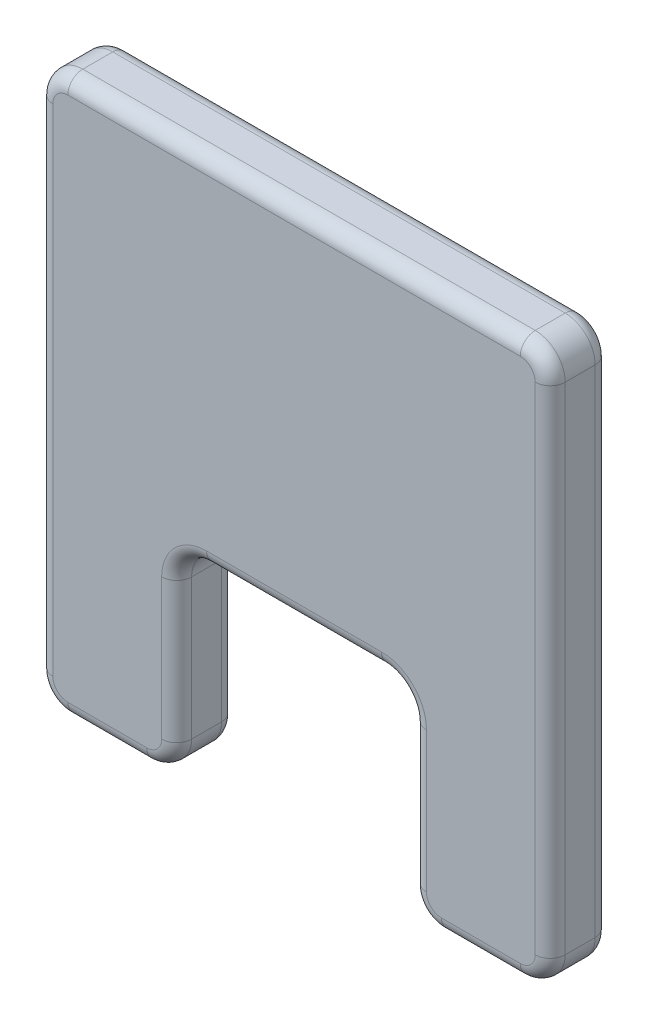
SolidWorks part; units mm, degrees
material "Polyurethane Foam Flexible"
ref_plane "Front Plane" through (0, 0, 0) normal (0, 0, 1) x (1, 0, 0)
ref_plane "Top Plane" through (0, 0, 0) normal (0, 1, 0) x (1, 0, 0)
ref_plane "Right Plane" through (0, 0, 0) normal (1, 0, 0) x (0, 0, -1)
sketch "Sketch1" plane through (0, 0, 0) normal (0, 0, 1) x (1, 0, 0)
  line L0 (-93.2955, 250.6666) -> (-93.2955, -223.9129) construction
  line L1 (-93.2955, 241.2246) -> (341.3045, 241.2246)
  line L2 (-93.2955, 241.2246) -> (-93.2955, -230.2629)
  line L3 (-93.2955, -230.2629) -> (24.3822, -230.2629)
  line L4 (341.3045, 241.2246) -> (341.3045, -230.2629)
  line L5 (223.6267, -230.2629) -> (341.3045, -230.2629)
  line L7 (24.3822, -230.2629) -> (24.3822, -60.2629)
  line L8 (24.3822, -60.2629) -> (223.6267, -60.2629)
  line L9 (223.6267, -230.2629) -> (223.6267, -60.2629)
  line L10 (24.3822, -223.9129) -> (24.3822, -60.2629) construction
  line L11 (16.7045, -230.2629) -> (-93.2955, -230.2629) construction
  line L12 (341.3045, -223.9129) -> (341.3045, 250.6666) construction
  dimension "D1" = 471.4875
extrude "Boss-Extrude1" add sketch "Sketch1" along normal blind 50.8
fillet "Fillet1" radius 25.4 8 edges at (24.3822, -230.2629, 25.4) (-93.2955, -230.2629, 25.4) (-93.2955, 241.2246, 25.4) (341.3045, 241.2246, 25.4) (341.3045, -230.2629, 25.4) (223.6267, -230.2629, 25.4) (223.6267, -60.2629, 25.4) (24.3822, -60.2629, 25.4)
fillet "Fillet2" radius 12.7 32 edges at (31.8217, -67.7023, 0) (124.0045, -60.2629, 0) (216.1872, -67.7023, 0) (223.6267, -145.2629, 0) (231.0662, -222.8234, 0) (282.4656, -230.2629, 0) (333.865, -222.8234, 0) (341.3045, 5.4809, 0) (333.865, 233.7852, 0) (124.0045, 241.2246, 0) (-85.856, 233.7852, 0) (-93.2955, 5.4809, 0) (-85.856, -222.8234, 0) (-34.4566, -230.2629, 0) (16.9428, -222.8234, 0) (24.3822, -145.2629, 0) (-85.856, -222.8234, 50.8) (-93.2955, 5.4809, 50.8) (-85.856, 233.7852, 50.8) (124.0045, 241.2246, 50.8) (333.865, 233.7852, 50.8) (341.3045, 5.4809, 50.8) (333.865, -222.8234, 50.8) (282.4656, -230.2629, 50.8) (231.0662, -222.8234, 50.8) (223.6267, -145.2629, 50.8) (216.1872, -67.7023, 50.8) (124.0045, -60.2629, 50.8) (31.8217, -67.7023, 50.8) (24.3822, -145.2629, 50.8) (16.9428, -222.8234, 50.8) (-34.4566, -230.2629, 50.8)
